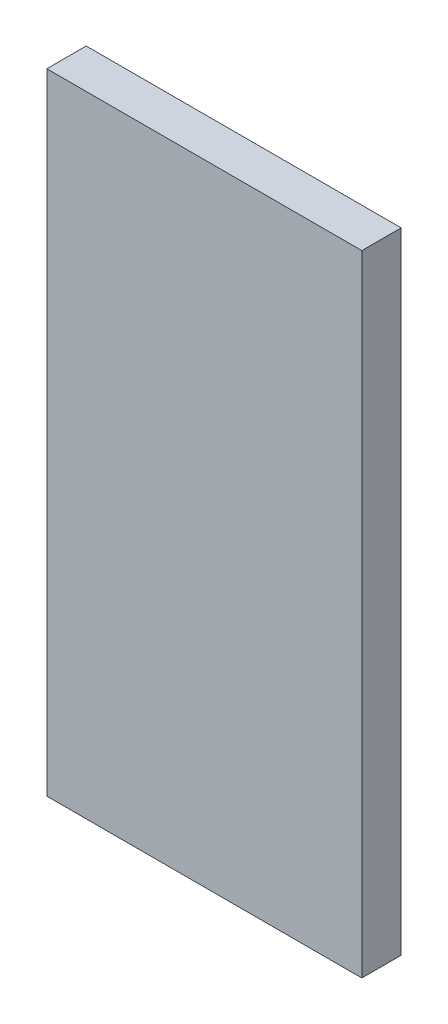
SolidWorks part; units mm, degrees
ref_plane "Front" through (0, 0, 0) normal (0, 0, 1) x (1, 0, 0)
ref_plane "Top" through (0, 0, 0) normal (0, 1, 0) x (1, 0, 0)
ref_plane "Right" through (0, 0, 0) normal (1, 0, 0) x (0, 0, -1)
sketch "Sketch1" plane through (0, 0, 0) normal (0, 0, 1) x (1, 0, 0)
  line L1 (12.7, -25.4) -> (-12.7, -25.4)
  line L2 (12.7, -25.4) -> (12.7, 25.4)
  line L3 (12.7, 25.4) -> (-12.7, 25.4)
  line L4 (-12.7, -25.4) -> (-12.7, 25.4)
  line L5 (12.7, -25.4) -> (-12.7, 25.4) construction
  line L6 (12.7, 25.4) -> (-12.7, -25.4) construction
  point P0 (0, 0)
  dimension "D1" = 25.4
  dimension "D2" = 50.8
extrude "Boss-Extrude1" add sketch "Sketch1" along normal mid plane 3.175
